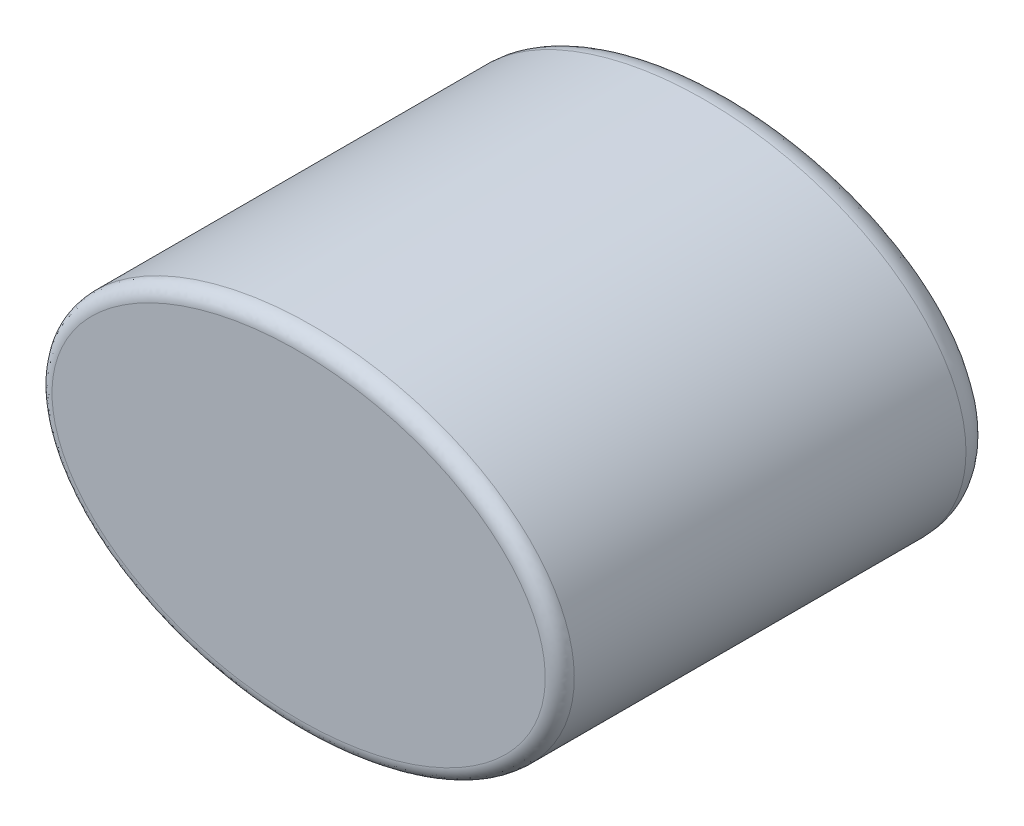
SolidWorks part; units mm, degrees
ref_plane "Front Plane" through (0, 0, 0) normal (0, 0, 1) x (1, 0, 0)
ref_plane "Top Plane" through (0, 0, 0) normal (0, 1, 0) x (1, 0, 0)
ref_plane "Right Plane" through (0, 0, 0) normal (1, 0, 0) x (0, 0, -1)
sketch "Sketch1" plane through (0, 0, 0) normal (0, 0, 1) x (1, 0, 0)
  ellipse E0 centre (0, 0) end of major axis (-22.86, 0) minor radius 15.24
extrude "Boss-Extrude4" add sketch "Sketch1" along normal blind 45.72 contours E0
sketch "Sketch4" plane through (0, 0, 45.72) normal (0, 0, 1) x (1, 0, 0)
  line L1 (14.605, -8.89) -> (-14.605, -8.89)
  line L2 (14.605, -8.89) -> (14.605, 8.89)
  line L3 (14.605, 8.89) -> (-14.605, 8.89)
  line L4 (-14.605, -8.89) -> (-14.605, 8.89)
  dimension "D1" = 8.89
  dimension "D2" = 17.78
  dimension "D3" = 14.605
  dimension "D4" = 29.21
extrude "Cut-Extrude2" cut sketch "Sketch4" against normal blind 33.02 from offset 10.16 offset against normal yes
sketch "Sketch7" plane through (0, 0, 0) normal (1, 0, 0) x (0, 0, -1)
  line L0 (-45.72, 15.24) -> (-45.72, -15.24) construction
  line L1 (-38.1, 16.1024) -> (-52.7439, 16.1024)
  line L2 (-38.1, 16.1024) -> (-38.1, -19.4576)
  line L3 (-38.1, -19.4576) -> (-52.7439, -19.4576)
  line L4 (-52.7439, 16.1024) -> (-52.7439, -19.4576)
  dimension "D1" = 7.62
  dimension "D2" = 14.6439
  dimension "D3" = 35.56
extrude "Cut-Extrude4" cut sketch "Sketch7" against normal blind 33.02 and the other way blind 33.02
sketch "Sketch8" plane through (0, 0, 0) normal (0, 0, 1) x (1, 0, 0)
  circle A0 centre (0, 0) radius 1.75
  circle A1 centre (4.064, 0) radius 1.75
  circle A2 centre (-4.064, 0) radius 1.75
extrude "Cut-Extrude5" cut sketch "Sketch8" along normal blind 1.27
sketch "Sketch9" plane through (0, 0, 0) normal (0, 0, -1) x (-1, 0, 0)
  circle A0 centre (0, 0.8) radius 0.5
  circle A1 centre (0, -0.8) radius 0.5
  circle A2 centre (-4.064, 0.8) radius 0.5
  circle A3 centre (-4.064, -0.8) radius 0.5
  circle A4 centre (4.064, 0.8) radius 0.5
  circle A5 centre (4.064, -0.8) radius 0.5
  point P4 (0, 0)
  point P9 (-4.064, -0.8)
  point P10 (-4.064, 0.8)
  point P11 (0, 0)
  point P16 (0, 0)
  point P17 (4.0477, 0.8)
  point P18 (4.064, -0.8)
  point P19 (0, 0)
  point P20 (0, 0)
  point P21 (4.064, 0.8)
extrude "Cut-Extrude7" cut sketch "Sketch9" against normal blind 2.794
fillet "Fillet1" radius 2.54 1 edges at (-22.86, 0, 0)
fillet "Fillet2" radius 1.27 1 edges at (-22.86, 0, 38.1)
